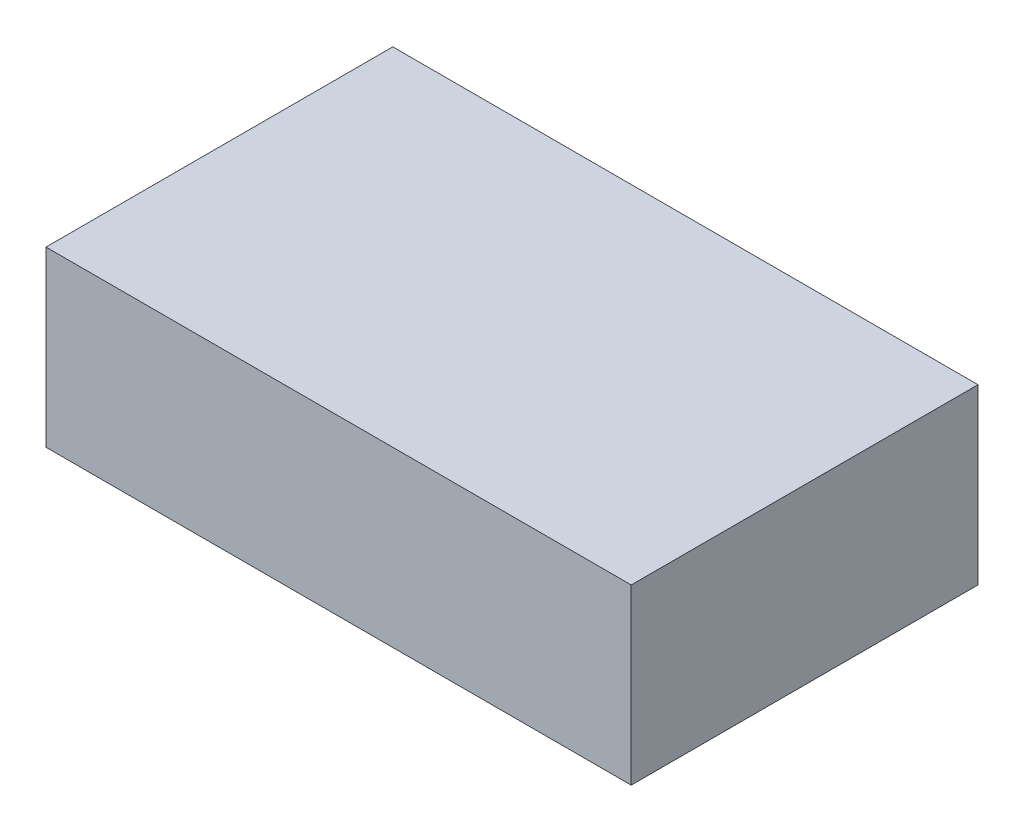
SolidWorks part; units mm, degrees
ref_plane "Front Plane" through (0, 0, 0) normal (0, 0, 1) x (1, 0, 0)
ref_plane "Top Plane" through (0, 0, 0) normal (0, 1, 0) x (1, 0, 0)
ref_plane "Right Plane" through (0, 0, 0) normal (1, 0, 0) x (0, 0, -1)
sketch "Sketch1" plane through (0, 0, 0) normal (0, 1, 0) x (1, 0, 0)
  line L1 (-85.725, -50.8) -> (85.725, -50.8)
  line L2 (-85.725, -50.8) -> (-85.725, 50.8)
  line L3 (-85.725, 50.8) -> (85.725, 50.8)
  line L4 (85.725, -50.8) -> (85.725, 50.8)
  line L5 (-85.725, -50.8) -> (85.725, 50.8) construction
  line L6 (-85.725, 50.8) -> (85.725, -50.8) construction
  point P0 (0, 0)
  dimension "D1" = 171.45
  dimension "D2" = 101.6
extrude "Boss-Extrude1" add sketch "Sketch1" along normal mid plane 50.8
